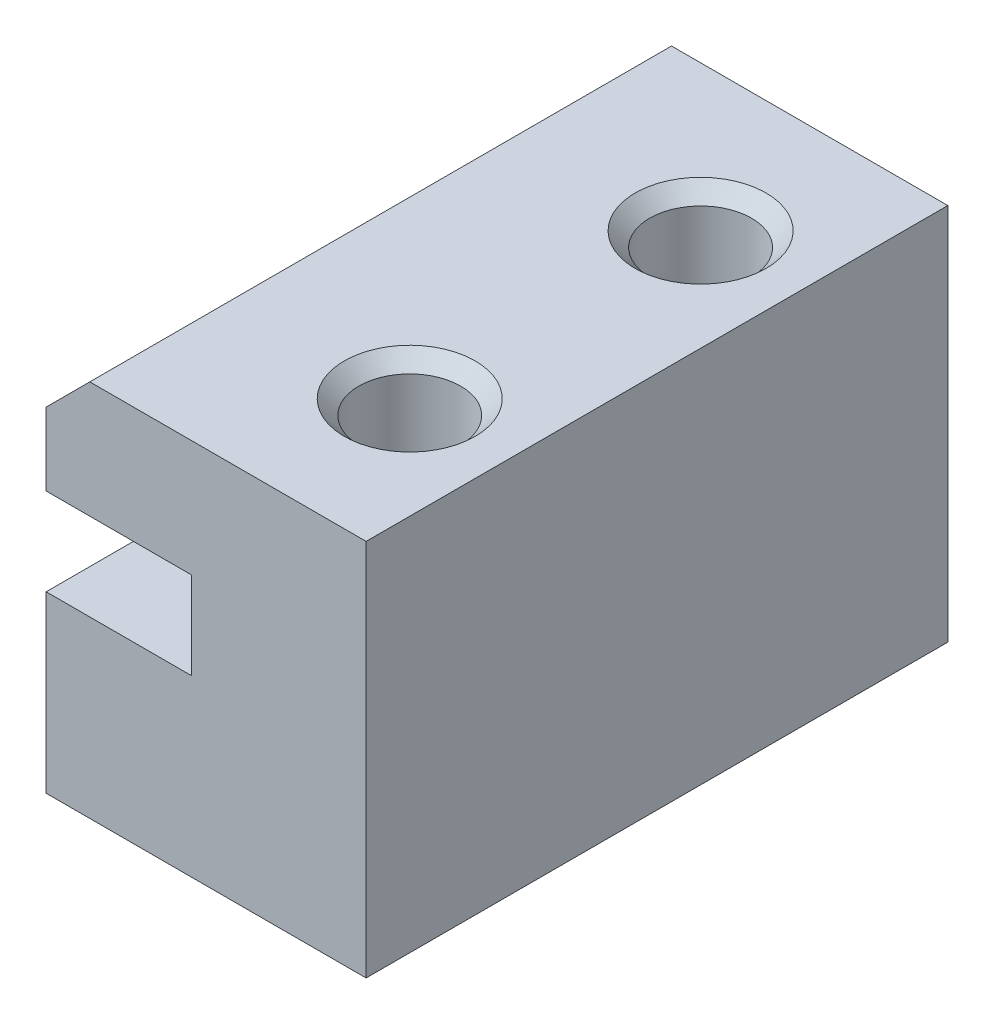
SolidWorks part; units mm, degrees
ref_plane "Front Plane" through (0, 0, 0) normal (0, 0, 1) x (1, 0, 0)
ref_plane "Top Plane" through (0, 0, 0) normal (0, 1, 0) x (1, 0, 0)
ref_plane "Right Plane" through (0, 0, 0) normal (1, 0, 0) x (0, 0, -1)
sketch "Sketch1" plane through (0, 0, 0) normal (0, 0, 1) x (1, 0, 0)
  line L0 (0, 0) -> (15, 0)
  line L5 (15, 0) -> (15, 6)
  line L6 (15, 6) -> (10, 6)
  line L11 (10, 6) -> (10, 9)
  line L12 (10, 9) -> (15, 9)
  line L17 (15, 9) -> (15, 13)
  line L18 (15, 13) -> (0, 13)
  line L19 (0, 13) -> (0, 9)
  line L20 (0, 9) -> (5, 9)
  line L21 (5, 9) -> (5, 6)
  line L22 (5, 6) -> (0, 6)
  line L23 (0, 6) -> (0, 0)
  line L24 (5, 6) -> (10, 6) construction
  line L25 (10, 9) -> (5, 9) construction
  line L26 (0, 9) -> (0, 6) construction
  line L27 (15, 6) -> (15, 9) construction
  point P3 (5, 7.5)
  dimension "D1" = 6
  dimension "D2" = 3
  dimension "D3" = 4
  dimension "D4" = 5
  dimension "D5" = 5
extrude "Boss-Extrude1" add sketch "Sketch1" along normal mid plane 20
sketch "Sketch2" plane through (0, 13, 0) normal (0, 1, 0) x (1, 0, 0)
  line L0 (7.5, -10) -> (7.5, -5) construction
  line L1 (7.5, -5) -> (7.5, 0) construction
  line L2 (7.5, 0) -> (7.5, 5) construction
  line L3 (7.5, 5) -> (7.5, 10) construction
  line L4 (15, 10) -> (0, 10)
  line L5 (0, 10) -> (0, -10)
  line L6 (0, -10) -> (15, -10)
  line L7 (15, -10) -> (15, 10)
  line L8 (15, 10) -> (0, 10)
  line L9 (0, 10) -> (0, -10)
  line L10 (0, -10) -> (15, -10)
  line L11 (15, -10) -> (15, 10)
  line L12 (0, 0) -> (7.5, 0) construction
  circle A0 centre (7.5, 5) radius 1.75
  circle A1 centre (7.5, -5) radius 1.75
  point P13 (0, 0)
  dimension "D2" = 3.5
  dimension "D1" = 0
extrude "Cut-Extrude1" cut sketch "Sketch2" against normal through all contours A1 | A0
chamfer "Chamfer1" distance 1.5 angle 45 2 edges at (0, 13, 0) (15, 13, 0)
sketch "Sketch3" plane through (0, 0, 10) normal (0, 0, 1) x (1, 0, 0)
  line L0 (13.5, 13) -> (1.5, 13) construction
  line L1 (10, 13) -> (15, 13)
  line L2 (10, 13) -> (10, 0)
  line L3 (10, 0) -> (15, 0)
  line L4 (15, 13) -> (15, 0)
  line L5 (10, 6) -> (10, 9) construction
  point P6 (13.8872, 1.0134)
extrude "Cut-Extrude2" cut sketch "Sketch3" against normal through all
sketch "Sketch4" plane through (10, 0, 0) normal (1, 0, 0) x (0, 0, -1)
  line L4 (10, 0) -> (10, 13)
  line L5 (10, 13) -> (-10, 13)
  line L6 (-10, 13) -> (-10, 0)
  line L7 (-10, 0) -> (10, 0)
  line L8 (10, 0) -> (10, 13)
  line L9 (10, 13) -> (-10, 13)
  line L10 (-10, 13) -> (-10, 0)
  line L11 (-10, 0) -> (10, 0)
  dimension "D1" = 0
extrude "Boss-Extrude2" add sketch "Sketch4" along normal blind 1
chamfer "Chamfer3" distance 0.5 angle 45 2 edges at (5.75, 13, -5) (5.75, 13, 5)
